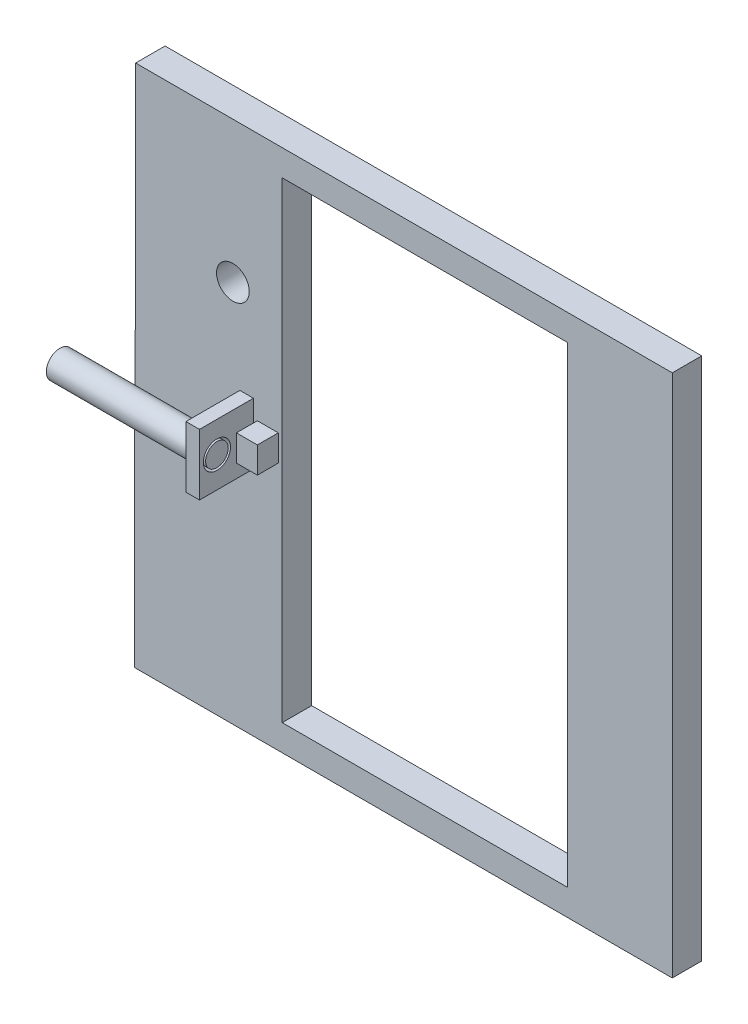
SolidWorks part; units mm, degrees
ref_plane "Front Plane" through (0, 0, 0) normal (0, 0, 1) x (1, 0, 0)
ref_plane "Top Plane" through (0, 0, 0) normal (0, 1, 0) x (1, 0, 0)
ref_plane "Right Plane" through (0, 0, 0) normal (1, 0, 0) x (0, 0, -1)
sketch "Sketch1" plane through (0, 0, 0) normal (0, 0, 1) x (1, 0, 0)
  line L1 (-69.215, -114.4587) -> (69.215, -114.4587)
  line L2 (-69.215, -114.4587) -> (-69.215, 114.4587)
  line L3 (-69.215, 114.4587) -> (69.215, 114.4587)
  line L4 (69.215, -114.4587) -> (69.215, 114.4587)
  line L5 (-69.215, -114.4587) -> (69.215, 114.4587) construction
  line L6 (-69.215, 114.4587) -> (69.215, -114.4587) construction
  line L11 (120.015, 127.127) -> (-83.185, 127.127)
  line L12 (120.015, 127.127) -> (120.015, -127.127)
  line L13 (120.015, -127.127) -> (-83.185, -127.127)
  line L14 (-83.185, 127.127) -> (-83.185, -127.127)
  point P0 (0, 0)
  point P6 (0, 0)
  dimension "D1" = 228.9175
  dimension "D2" = 138.43
  dimension "D3" = 50.8
  dimension "D4" = 203.2
  dimension "D5" = 254.254
  dimension "D6" = 127.127
extrude "Boss-Extrude1" add sketch "Sketch1" along normal blind 1.5875 and the other way blind 12.7
sketch "Sketch2" plane through (0, 0, 1.5875) normal (0, 0, 1) x (1, 0, 0)
  line L0 (-83.185, 127.127) -> (-83.185, -127.127) construction
  line L1 (-81.28, -6.35) -> (-71.12, -6.35)
  line L2 (-81.28, -6.35) -> (-81.28, 6.35)
  line L3 (-81.28, 6.35) -> (-71.12, 6.35)
  line L4 (-71.12, -6.35) -> (-71.12, 6.35)
  line L5 (-81.28, -6.35) -> (-71.12, 6.35) construction
  line L6 (-81.28, 6.35) -> (-71.12, -6.35) construction
  point P0 (-76.2, 0)
  dimension "D1" = 10.16
  dimension "D2" = 12.7
  dimension "D3" = 1.905
  dimension "D4" = 6.35
extrude "Boss-Extrude2" add sketch "Sketch2" along normal blind 10.16
sketch "Sketch3" plane through (-83.185, 0, 0) normal (-1, 0, 0) x (0, 0, 1)
  line L0 (1.5875, 127.127) -> (1.5875, -127.127) construction
  line L1 (-13.6525, -14.8345) -> (1.5875, -14.8345)
  line L2 (-13.6525, -14.8345) -> (-13.6525, 14.8592)
  line L3 (-13.6525, 14.8592) -> (1.5875, 14.8592)
  line L4 (1.5875, -14.8345) -> (1.5875, 14.8592)
  line L5 (-13.6525, -14.8345) -> (1.5875, 14.8592) construction
  line L6 (-13.6525, 14.8592) -> (1.5875, -14.8345) construction
  point P0 (-6.0325, 0.0124)
  dimension "D1" = 15.24
extrude "Boss-Extrude3" add sketch "Sketch3" along normal blind 6.5789
sketch "Sketch5" plane through (0, 0, 1.5875) normal (0, 0, 1) x (1, 0, 0)
  line L1 (-89.7639, 14.8592) -> (-83.185, 14.8592)
  line L2 (-89.7639, 14.8592) -> (-89.7639, -14.8345)
  line L3 (-89.7639, -14.8345) -> (-83.185, -14.8345)
  line L4 (-83.185, 14.8592) -> (-83.185, -14.8345)
extrude "Boss-Extrude4" add sketch "Sketch5" along normal blind 26.162
sketch "Sketch6" plane through (-83.185, 0, 0) normal (1, 0, 0) x (0, 0, -1)
  circle A0 centre (-19.2912, 0) radius 6.604
extrude "Boss-Extrude6" add sketch "Sketch6" against normal blind 76.2
sketch "Sketch11" plane through (-83.185, 0, 0) normal (1, 0, 0) x (0, 0, -1)
  circle A0 centre (-19.2912, 0) radius 6.604
  circle A1 centre (-19.2912, 0) radius 5.4991
extrude "Cut-Extrude3" cut sketch "Sketch11" against normal blind 5.842 contours A0
sketch "Sketch13" plane through (-89.027, 0, 0) normal (1, 0, 0) x (0, 0, -1)
  circle A0 centre (-19.2912, 0) radius 5.4991
extrude "Boss-Extrude7" add sketch "Sketch13" along normal blind 5.842
sketch "Sketch15" plane through (-89.7639, 0, 0) normal (-1, 0, 0) x (0, 0, 1)
  line L1 (-13.6525, 14.8592) -> (1.5875, 14.8592)
  line L2 (-13.6525, 14.8592) -> (-13.6525, -14.8345)
  line L3 (-13.6525, -14.8345) -> (1.5875, -14.8345)
  line L4 (1.5875, 14.8592) -> (1.5875, -14.8345)
extrude "Boss-Extrude8" add sketch "Sketch15" along normal blind 50.8
sketch "Sketch16" plane through (-83.185, 0, 0) normal (-1, 0, 0) x (0, 0, 1)
  line L1 (-12.7, 127.127) -> (1.5875, 127.127)
  line L2 (-12.7, 127.127) -> (-12.7, 14.8592)
  line L3 (-12.7, 14.8592) -> (1.5875, 14.8592)
  line L4 (1.5875, 127.127) -> (1.5875, 14.8592)
extrude "Boss-Extrude9" add sketch "Sketch16" along normal blind 57.15
sketch "Sketch17" plane through (-83.185, 0, 0) normal (-1, 0, 0) x (0, 0, 1)
  line L0 (1.5875, -14.8345) -> (1.5875, -127.127) construction
  line L1 (-12.7, -14.8345) -> (1.5875, -14.8345)
  line L2 (-12.7, -14.8345) -> (-12.7, -127.127)
  line L3 (-12.7, -127.127) -> (1.5875, -127.127)
  line L4 (1.5875, -14.8345) -> (1.5875, -127.127)
  line L5 (-12.7, -127.127) -> (1.5875, -127.127) construction
extrude "Boss-Extrude10" add sketch "Sketch17" along normal blind 57.658
sketch "Sketch18" plane through (0, 0, 1.5875) normal (0, 0, 1) x (1, 0, 0)
  circle A0 centre (-93.1412, 58.5901) radius 7.9375
extrude "Cut-Extrude4" cut sketch "Sketch18" against normal blind 57.658
